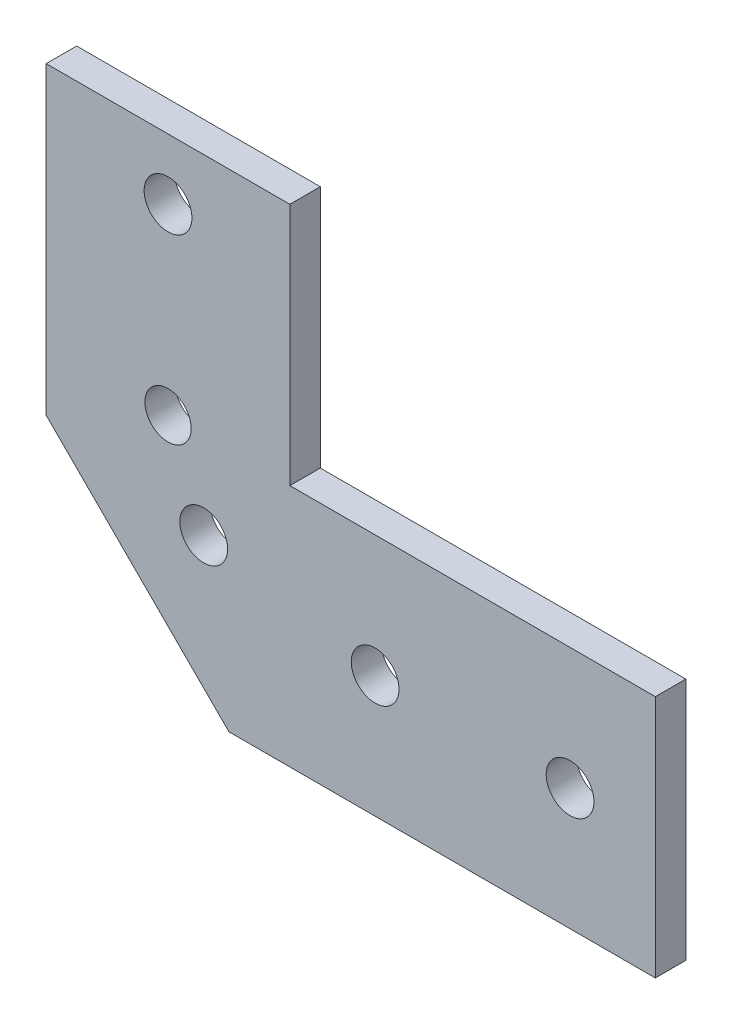
SolidWorks part; units mm, degrees
ref_plane "Front Plane" through (0, 0, 0) normal (0, 0, 1) x (1, 0, 0)
ref_plane "Top Plane" through (0, 0, 0) normal (0, 1, 0) x (1, 0, 0)
ref_plane "Right Plane" through (0, 0, 0) normal (1, 0, 0) x (0, 0, -1)
sketch "Sketch2" plane through (0, 0, 0) normal (0, 0, 1) x (1, 0, 0)
  line L0 (0, 0) -> (0, 63.5)
  line L1 (0, 0) -> (63.5, 0)
  line L2 (63.5, 0) -> (63.5, 25.4)
  line L3 (63.5, 25.4) -> (25.4, 25.4)
  line L4 (25.4, 25.4) -> (25.4, 63.5)
  line L5 (25.4, 63.5) -> (0, 63.5)
  dimension "D1" = 25.4
  dimension "D2" = 25.4
  dimension "D3" = 63.5
  dimension "D4" = 63.5
extrude "Boss-Extrude1" add sketch "Sketch2" along normal blind 3.175
sketch "Sketch3" plane through (0, 0, 3.175) normal (0, 0, 1) x (1, 0, 0)
  line L0 (0, 0) -> (0, 19.05)
  line L1 (0, 63.5) -> (0, 0) construction
  line L4 (0, 0) -> (63.5, 0) construction
  line L5 (19.05, 0) -> (0, 0)
  line L6 (19.05, 0) -> (0, 19.05)
  line L7 (25.4, 25.4) -> (0, 25.4) construction
  line L8 (12.7, 54.61) -> (25.4, 54.61) construction
  line L9 (25.4, 34.29) -> (25.4, 25.4) construction
  line L10 (12.7, 34.29) -> (25.4, 34.29) construction
  line L11 (25.4, 25.4) -> (25.4, 63.5) construction
  line L12 (25.4, 54.61) -> (25.4, 63.5) construction
  line L13 (12.7, 44.45) -> (25.4, 44.45) construction
  line L14 (12.7, 44.45) -> (12.7, 54.61) construction
  line L15 (12.7, 44.45) -> (12.7, 34.29) construction
  line L22 (25.4, 25.4) -> (7.4395, 7.4395) construction
  circle A17 centre (16.4197, 16.4197) radius 2.4892
  circle A18 centre (12.7, 54.61) radius 2.4892
  circle A19 centre (12.7, 44.45) radius 2.4892
  circle A20 centre (12.7, 34.29) radius 2.4892 construction
  circle A21 centre (34.29, 12.7) radius 2.4892
  circle A22 centre (44.45, 12.7) radius 2.4892 construction
  circle A23 centre (54.61, 12.7) radius 2.4892
  dimension "D3" = 4.9784
  dimension "D5" = 4.9784
  dimension "D4" = 12.7
  dimension "D7" = 8.89
  dimension "D1" = 45
  dimension "D2" = 19.05
  dimension "D6" = 12.7
  dimension "D8" = 90
extrude "Cut-Extrude1" cut sketch "Sketch3" against normal through all
sketch "Sketch4" plane through (0, 0, 0) normal (0, 0, -1) x (-1, 0, 0)
  line L0 (-25.4, 25.4) -> (-25.4, 63.5) construction
  circle A1 centre (-12.7, 25.4) radius 2.413
  dimension "D3" = 4.826
  dimension "D1" = 12.7
  dimension "D2" = 6.35
extrude "Cut-Extrude2" cut sketch "Sketch4" against normal through all
sketch "Sketch5" plane through (0, 0, 3.175) normal (0, 0, 1) x (1, 0, 0)
  line L0 (0, 50.8) -> (25.4, 50.8)
  line L1 (0, 63.5) -> (0, 19.05) construction
  line L2 (25.4, 25.4) -> (25.4, 63.5) construction
  line L3 (25.4, 50.8) -> (25.4, 63.5)
  line L4 (25.4, 63.5) -> (0, 63.5)
  line L5 (0, 63.5) -> (0, 50.8)
  circle A0 centre (12.7, 44.45) radius 2.4892 construction
  dimension "D1" = 6.35
extrude "Cut-Extrude3" cut sketch "Sketch5" against normal through all
